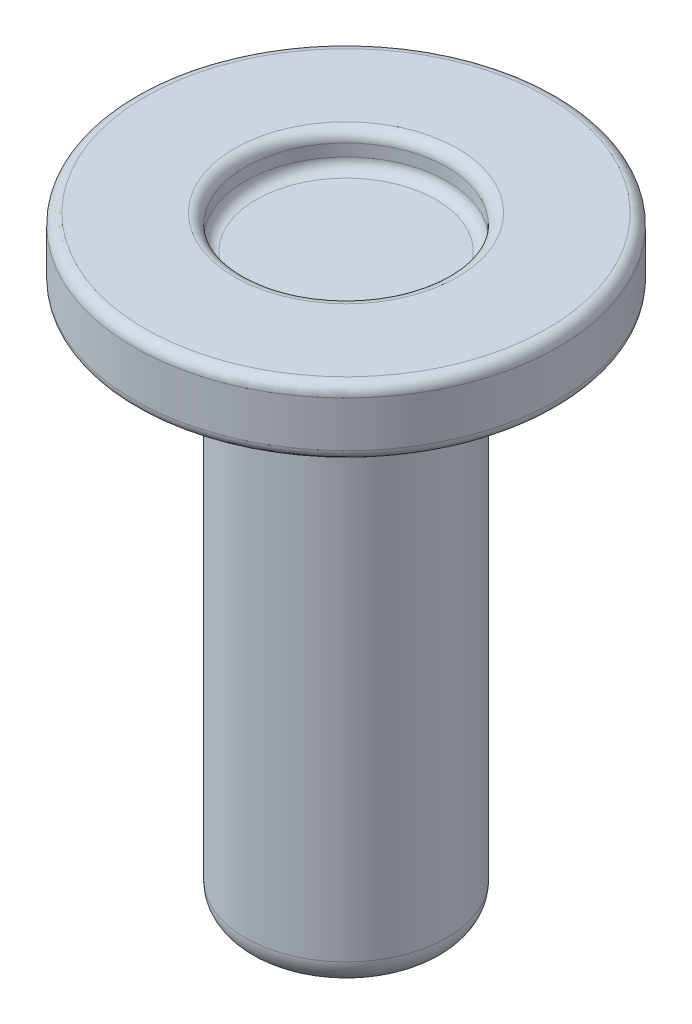
SolidWorks part; units mm, degrees
ref_plane "Front Plane" through (0, 0, 0) normal (0, 0, 1) x (1, 0, 0)
ref_plane "Top Plane" through (0, 0, 0) normal (0, 1, 0) x (1, 0, 0)
ref_plane "Right Plane" through (0, 0, 0) normal (1, 0, 0) x (0, 0, -1)
sketch "Sketch1" plane through (0, 0, 0) normal (0, 0, 1) x (1, 0, 0)
  line L0 (0, 0) -> (-2.1273, 0)
  line L1 (-2.3813, 0.254) -> (-2.3813, 0.5397)
  line L2 (-2.6353, 0.7937) -> (-4.7498, 0.7937)
  line L3 (-5.0038, 0.5397) -> (-5.0038, -0.5397)
  line L4 (-4.7498, -0.7938) -> (-2.6353, -0.7938)
  line L5 (-2.3813, -1.0478) -> (-2.3813, -12.8587)
  line L6 (-1.7462, -13.4938) -> (0, -13.4938)
  line L7 (0, -13.4938) -> (0, 0)
  arc A1 (-1.7462, -13.4938) -> (-2.3813, -12.8587) centre (-1.7463, -12.8588) cw
  arc A2 (-2.3813, -1.0478) -> (-2.6353, -0.7938) centre (-2.6353, -1.0478) ccw
  arc A3 (-2.1273, 0) -> (-2.3813, 0.254) centre (-2.1273, 0.254) cw
  arc A4 (-4.7498, -0.7938) -> (-5.0038, -0.5397) centre (-4.7498, -0.5398) cw
  arc A5 (-5.0038, 0.5397) -> (-4.7498, 0.7937) centre (-4.7498, 0.5397) cw
  arc A6 (-2.3813, 0.5397) -> (-2.6353, 0.7937) centre (-2.6353, 0.5397) ccw
  point P16 (0, -13.4938)
  point P19 (-2.3813, -13.4938)
  point P22 (-2.3813, -0.7938)
  point P25 (-2.3813, 0)
  point P28 (-5.0038, -0.7938)
  point P31 (-5.0038, 0.7937)
  dimension "D7" = 0.254
  dimension "D1" = 12.7
  dimension "D3" = 2.3813
  dimension "D4" = 1.5875
  dimension "D5" = 0.7937
  dimension "D2" = 5.0038
  dimension "D6" = 0.635
revolve "Revolve1" add sketch "Sketch1" angle 360 about L7
equation "\"D3@Sketch1\"=3/32"
equation "\"D5@Sketch1\"=\"D4@Sketch1\"/2"
